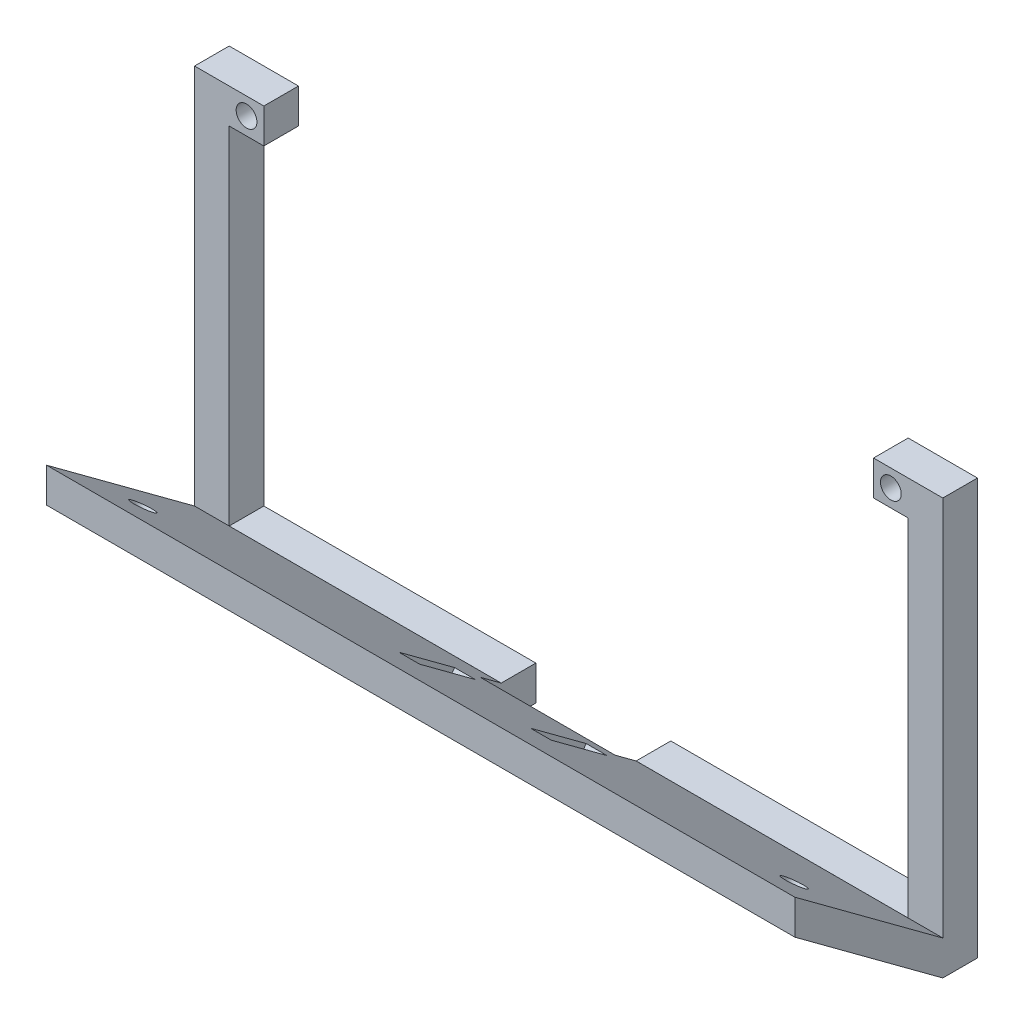
SolidWorks part; units mm, degrees
ref_plane "Front Plane" through (0, 0, 0) normal (0, 0, 1) x (1, 0, 0)
ref_plane "Top Plane" through (0, 0, 0) normal (0, 1, 0) x (1, 0, 0)
ref_plane "Right Plane" through (0, 0, 0) normal (1, 0, 0) x (0, 0, -1)
sketch "Sketch3" plane through (0, 0, 0) normal (0, 0, 1) x (1, 0, 0)
  line L0 (-46.5, 26) -> (-46.5, 27.5)
  line L1 (-46.5, -27.5) -> (-45, -27.5)
  line L2 (-46.5, -27.5) -> (-46.5, -26)
  line L3 (-46.5, 27.5) -> (-45, 27.5)
  line L5 (-46.5, -27.5) -> (-45.2089, -26.7364) construction
  line L6 (-46.5, 27.5) -> (-45.2089, 26.7364) construction
  line L7 (44, 26.9388) -> (45.0009, 27.5516) construction
  line L11 (47.1357, 28.8586) -> (49, 30) construction
  line L12 (-44, 25) -> (-44, 30)
  line L13 (-44, -25) -> (44, -25)
  line L17 (-44, -25) -> (44, 25) construction
  line L18 (-44, 25) -> (44, -25) construction
  line L19 (-49, -30) -> (49, -30)
  line L20 (-49, -25) -> (-49, 25)
  line L21 (-49, 30) -> (-44, 30)
  line L22 (49, -25) -> (49, 25)
  line L23 (-49, -30) -> (40.8333, 25) construction
  line L24 (-49, 30) -> (-44, 26.9388) construction
  line L25 (44, 25) -> (44, 30)
  line L26 (44, 30) -> (49, 30)
  line L28 (-40.8333, 25) -> (40.8333, -25) construction
  line L29 (-49, 30) -> (-54, 30)
  line L30 (-49, 25) -> (-49, -25)
  line L31 (-49, -30) -> (-54, -30)
  line L32 (-54, 30) -> (-54, -30)
  line L33 (49, -30) -> (54, -30)
  line L34 (49, -25) -> (49, 25)
  line L35 (49, 30) -> (54, 30)
  line L36 (54, -30) -> (54, 30)
  line L37 (44, 30) -> (54, 30)
  line L38 (44, 30) -> (44, 25)
  line L39 (44, 25) -> (49, 25)
  line L40 (54, 30) -> (54, 25)
  line L41 (44, -25) -> (49, -25)
  line L43 (44, -30) -> (54, -30)
  line L44 (54, -25) -> (54, -30)
  line L45 (-44, 25) -> (-49, 25)
  line L46 (-44, 25) -> (-44, 30)
  line L47 (-44, 30) -> (-54, 30)
  line L48 (-54, 25) -> (-54, 30)
  line L49 (-44, -25) -> (-49, -25)
  line L51 (-44, -30) -> (-54, -30)
  line L52 (-54, -25) -> (-54, -30)
  line L53 (44, -26.9388) -> (49, -30) construction
  circle A0 centre (-46.5, 27.5) radius 1.5
  circle A1 centre (46.5, 27.5) radius 1.5
  circle A2 centre (-46.5, -27.5) radius 1.5
  circle A3 centre (46.5, -27.5) radius 1.5
  point P0 (0, 0)
  point P27 (0, 0)
  dimension "D3" = 3
  dimension "D1" = 93
  dimension "D2" = 55
  dimension "D10" = 5
  dimension "D11" = 5
  dimension "D12" = 5
extrude "Boss-Extrude2" add sketch "Sketch3" along normal blind 5
sketch "Sketch4" plane through (54, 0, 0) normal (1, 0, 0) x (0, 0, -1)
  line L0 (-5, -30) -> (-5, -25.0015)
  line L1 (-5, -30) -> (-26.3639, -14.2132)
  line L2 (-5, -25.0015) -> (-26.3639, -9.2147)
  line L3 (-26.3639, -14.2132) -> (-26.3639, -9.2147)
  line L4 (-5, -30) -> (-5, 30) construction
  point P7 (-26.8746, -10.2803)
  point P9 (-5, -25.0015)
  dimension "D1" = 4.02
extrude "Boss-Extrude3" add sketch "Sketch4" against normal up to surface (108 mm away) up to face at (-54, 0, 2.5)
sketch "Sketch5" plane through (0, -21.7942, 16.1047) normal (0, -0.8042, 0.5943) x (-1, 0, 0)
  line L0 (0, 13.8076) -> (0, -12.7563) construction
  line L1 (-54, 13.8076) -> (54, 13.8076) construction
  line L2 (54, -12.7563) -> (-54, -12.7563) construction
  circle A0 centre (47, -7.1327) radius 1.6
  circle A1 centre (-47, -7.1327) radius 1.6
  point P11 (47, -7.1327)
  dimension "D1" = 47
  dimension "D2" = 3.2
extrude "Cut-Extrude1" cut sketch "Sketch5" against normal up to next
sketch "Sketch6" plane through (0, -21.7942, 16.1047) normal (0, -0.8042, 0.5943) x (-1, 0, 0)
  line L0 (0, -12.7563) -> (0, 13.8076) construction
  line L1 (54, -12.7563) -> (-54, -12.7563) construction
  line L2 (-54, 13.8076) -> (54, 13.8076) construction
  line L3 (-8, -5.9641) -> (-8, 4.0359)
  line L4 (11, -5.9641) -> (8, -5.9641)
  line L5 (11, -5.9641) -> (11, 4.0359)
  line L6 (11, 4.0359) -> (8, 4.0359)
  line L7 (8, -5.9641) -> (8, 4.0359)
  line L8 (-11, 4.0359) -> (-8, 4.0359)
  line L9 (-11, -5.9641) -> (-11, 4.0359)
  line L10 (-11, -5.9641) -> (-8, -5.9641)
  dimension "D1" = 10
  dimension "D2" = 3
  dimension "D3" = 8
extrude "Cut-Extrude2" cut sketch "Sketch6" against normal up to next
sketch "Sketch7" plane through (0, -30, 0) normal (0, -1, 0) x (-1, 0, 0)
  line L1 (-9.7363, 13.14) -> (9.7363, 13.14)
  line L2 (-9.7363, 13.14) -> (-9.7363, -8.0308)
  line L3 (-9.7363, -8.0308) -> (9.7363, -8.0308)
  line L4 (9.7363, 13.14) -> (9.7363, -8.0308)
  point P4 (0, 13.14)
extrude "Cut-Extrude3" cut sketch "Sketch7" against normal through all
